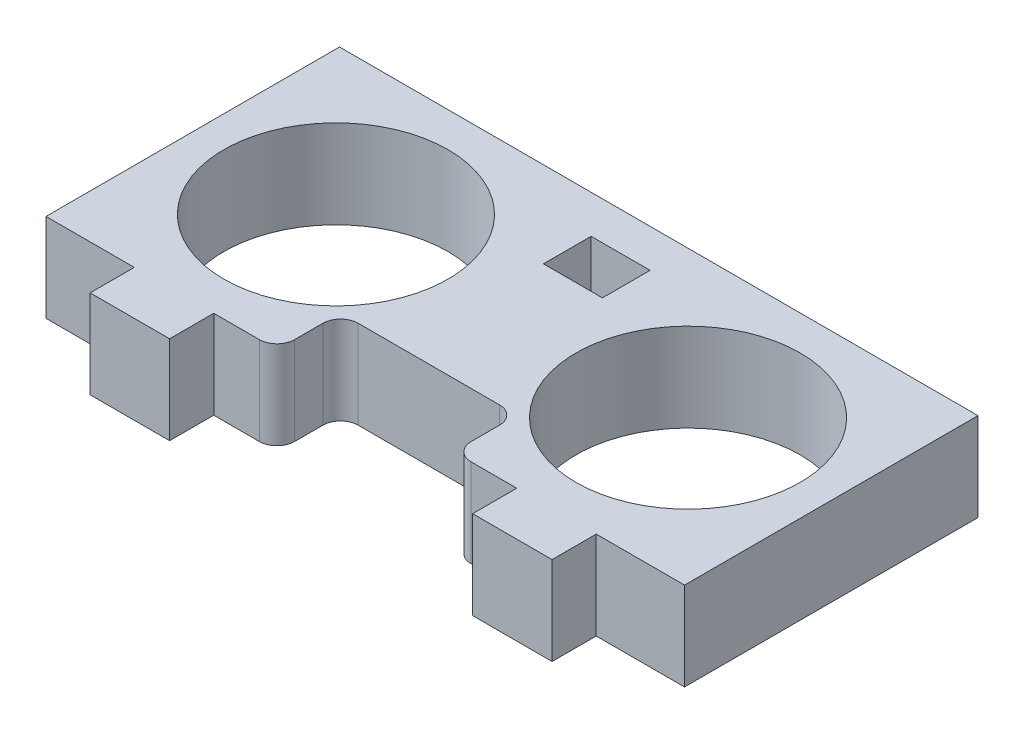
SolidWorks part; units mm, degrees
ref_plane "Front" through (0, 0, 0) normal (0, 0, 1) x (1, 0, 0)
ref_plane "Top" through (0, 0, 0) normal (0, 1, 0) x (1, 0, 0)
ref_plane "Right" through (0, 0, 0) normal (1, 0, 0) x (0, 0, -1)
sketch "Sketch1" plane through (0, 0, 0) normal (0, 1, 0) x (1, 0, 0)
  line L0 (-12.6619, 0) -> (0, 0) construction
  line L1 (-22.9616, 10.5537) -> (22.9616, 10.5537)
  line L2 (-22.9616, 10.5537) -> (-22.9616, -10.5537)
  line L3 (-22.9616, -10.5537) -> (22.9616, -10.5537)
  line L4 (22.9616, 10.5537) -> (22.9616, -10.5537)
  line L5 (-22.9616, 10.5537) -> (22.9616, -10.5537) construction
  line L6 (-22.9616, -10.5537) -> (22.9616, 10.5537) construction
  line L7 (0, 0) -> (12.6619, 0) construction
  circle A0 centre (-12.6619, 0) radius 8.0645
  circle A1 centre (12.6619, 0) radius 8.0645
  point P0 (0, 0)
  point P11 (-4.5974, 0)
  point P12 (4.5974, 0)
  dimension "D3" = 16.129
  dimension "D4" = 9.1948
  dimension "D1" = 45.9232
  dimension "D2" = 21.1074
extrude "Boss-Extrude1" add sketch "Sketch1" along normal blind 6.35
sketch "Sketch2" plane through (0, 6.35, 0) normal (0, 1, 0) x (1, 0, 0)
  line L0 (22.9616, 10.5537) -> (-22.9616, 10.5537) construction
  line L1 (-2.1209, 7.8105) -> (2.1209, 7.8105)
  line L2 (-2.1209, 7.8105) -> (-2.1209, 4.3815)
  line L3 (-2.1209, 4.3815) -> (2.1209, 4.3815)
  line L4 (2.1209, 7.8105) -> (2.1209, 4.3815)
  line L5 (-2.1209, 7.8105) -> (2.1209, 4.3815) construction
  line L6 (-2.1209, 4.3815) -> (2.1209, 7.8105) construction
  line L7 (0, 0) -> (0, 6.096) construction
  line L8 (-22.9616, -10.5537) -> (22.9616, -10.5537) construction
  line L9 (-6.35, -10.5537) -> (6.35, -10.5537)
  line L10 (-6.35, -10.5537) -> (-6.35, -5.9817)
  line L11 (-6.35, -5.9817) -> (6.35, -5.9817)
  line L12 (6.35, -10.5537) -> (6.35, -5.9817)
  line L13 (0, 0) -> (0, -5.9817) construction
  point P0 (0, 6.096)
  dimension "D1" = 4.2418
  dimension "D2" = 3.429
  dimension "D3" = 2.7432
  dimension "D4" = 12.7
  dimension "D5" = 4.572
extrude "Cut-Extrude1" cut sketch "Sketch2" against normal up to surface (6.35 mm away) up to face at (-12.6619, 0, 8.0645)
ref_plane "Plane1" through (-22.9616, 6.35, -10.5537) normal (0, 0, 1) x (1, 0, 0)
sketch "Sketch4" plane through (0, 6.35, 0) normal (0, 1, 0) x (1, 0, 0)
  line L0 (-22.9616, -10.5537) -> (-6.35, -10.5537) construction
  line L1 (-16.6116, -10.5537) -> (-10.8966, -10.5537)
  line L2 (-16.6116, -10.5537) -> (-16.6116, -13.7287)
  line L3 (-16.6116, -13.7287) -> (-10.8966, -13.7287)
  line L4 (-10.8966, -10.5537) -> (-10.8966, -13.7287)
  line L5 (6.35, -10.5537) -> (22.9616, -10.5537) construction
  line L6 (10.8966, -10.5537) -> (16.6116, -10.5537)
  line L7 (10.8966, -10.5537) -> (10.8966, -13.7287)
  line L8 (10.8966, -13.7287) -> (16.6116, -13.7287)
  line L9 (16.6116, -10.5537) -> (16.6116, -13.7287)
  line L10 (-22.9616, 10.5537) -> (-22.9616, -10.5537) construction
  line L11 (22.9616, -10.5537) -> (22.9616, 10.5537) construction
  dimension "D1" = 5.715
  dimension "D2" = 6.35
  dimension "D3" = 6.35
  dimension "D4" = 3.175
extrude "Boss-Extrude3" add sketch "Sketch4" against normal up to surface (6.35 mm away) up to face at (0, 0, -6.096)
fillet "Fillet1" radius 1.27 4 edges at (-6.35, 3.175, 5.9817) (6.35, 3.175, 5.9817) (6.35, 3.175, 10.5537) (-6.35, 3.175, 10.5537)
